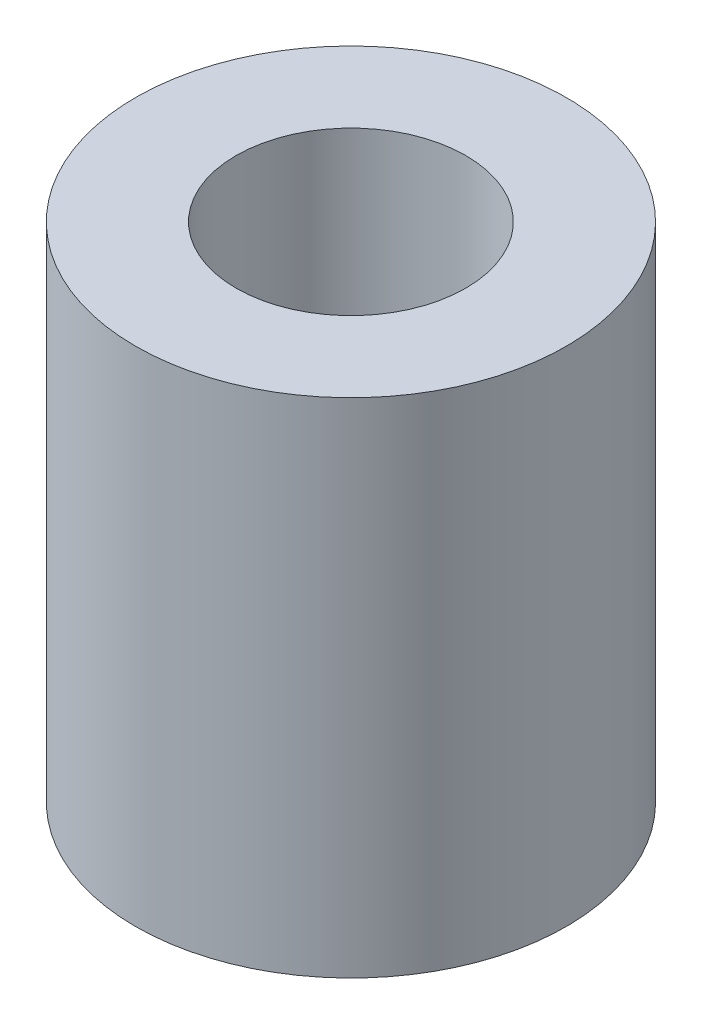
SolidWorks part; units mm, degrees
ref_plane "前视基准面" through (0, 0, 0) normal (0, 0, 1) x (1, 0, 0)
ref_plane "上视基准面" through (0, 0, 0) normal (0, 1, 0) x (1, 0, 0)
ref_plane "右视基准面" through (0, 0, 0) normal (1, 0, 0) x (0, 0, -1)
sketch "草图1" plane through (0, 0, 0) normal (0, 1, 0) x (1, 0, 0)
  circle A0 centre (0, 0) radius 3.5
  circle A1 centre (0, 0) radius 15
  dimension "D1" = 7
  dimension "D2" = 30
extrude "凸台-拉伸1" add sketch "草图1" along normal blind 35 contours A1 A0 | A0
sketch "草图2" plane through (0, 0, 0) normal (0, -1, 0) x (1, 0, 0)
  circle A0 centre (0, 0) radius 3.5
extrude "切除-拉伸1" cut sketch "草图2" against normal blind 10
sketch "草图3" plane through (0, 35, 0) normal (0, 1, 0) x (1, 0, 0)
  circle A0 centre (0, 0) radius 8
extrude "切除-拉伸2" cut sketch "草图3" against normal blind 32
